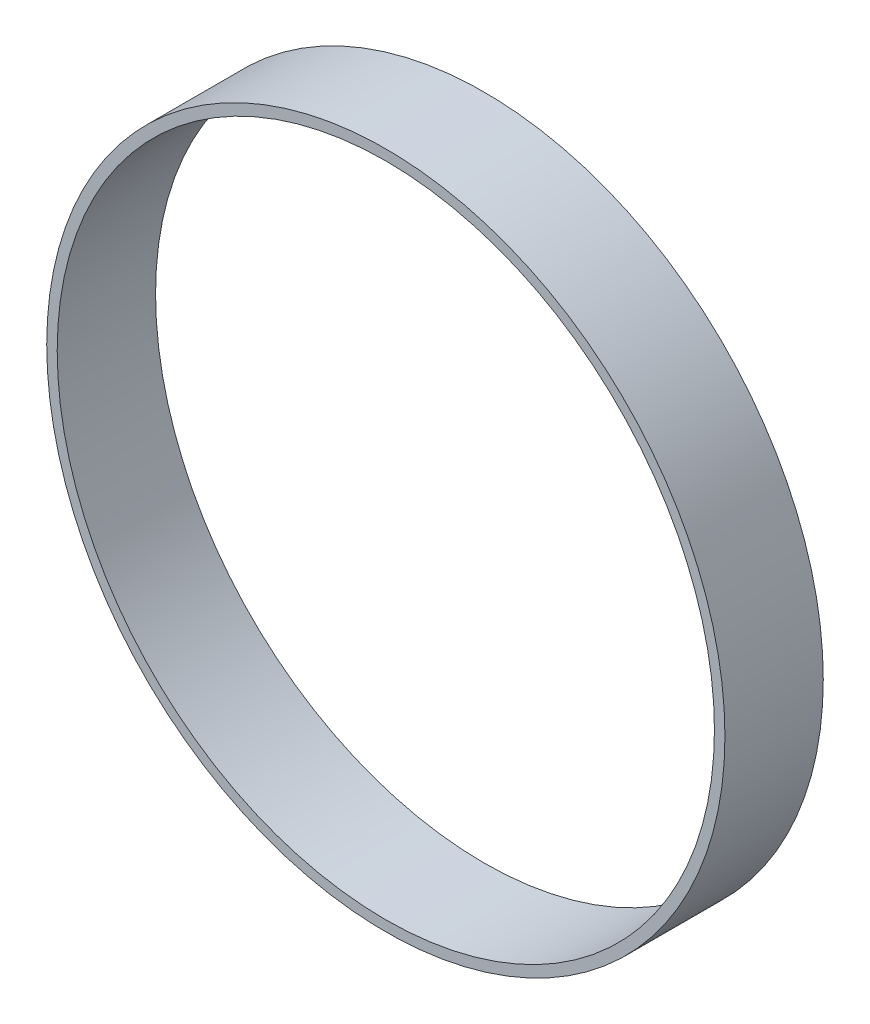
SolidWorks part; units mm, degrees
material "ABS PC"
ref_plane "Front Plane" through (0, 0, 0) normal (0, 0, 1) x (1, 0, 0)
ref_plane "Top Plane" through (0, 0, 0) normal (0, 1, 0) x (1, 0, 0)
ref_plane "Right Plane" through (0, 0, 0) normal (1, 0, 0) x (0, 0, -1)
sketch "Sketch1" plane through (0, 0, 0) normal (0, 0, 1) x (1, 0, 0)
  circle A0 centre (0, 0) radius 16.4211
  circle A1 centre (0, 0) radius 15.9131
  dimension "D1" = 32.8422
  dimension "D2" = 0.508
extrude "Boss-Extrude1" add sketch "Sketch1" along normal blind 4.7625
